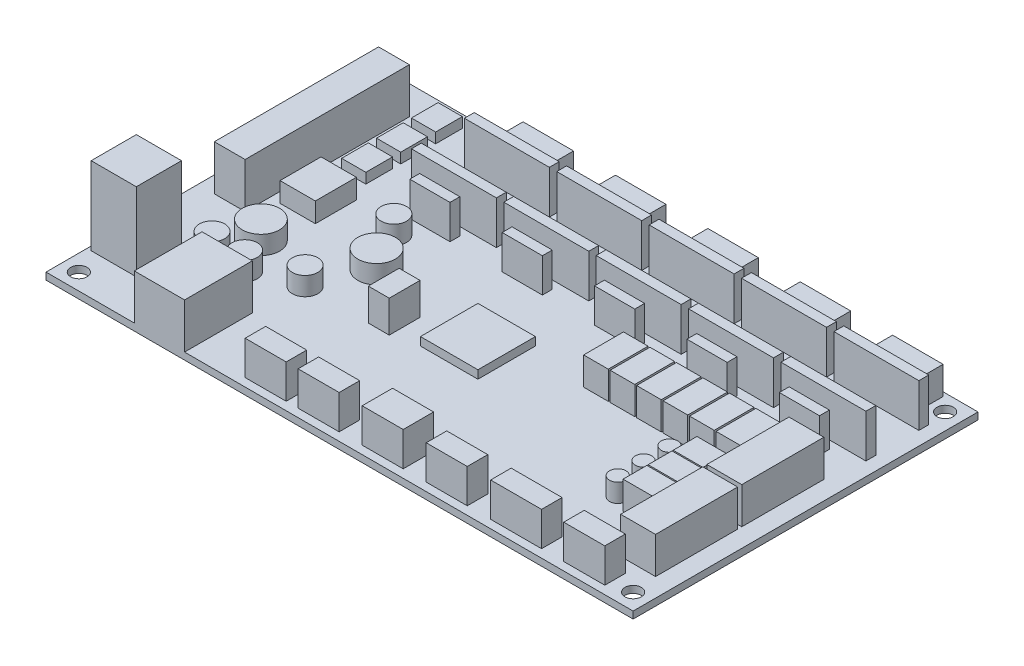
SolidWorks part; units mm, degrees
ref_plane "Front Plane" through (0, 0, 0) normal (0, 0, 1) x (1, 0, 0)
ref_plane "Top Plane" through (0, 0, 0) normal (0, 1, 0) x (1, 0, 0)
ref_plane "Right Plane" through (0, 0, 0) normal (1, 0, 0) x (0, 0, -1)
sketch "PCB" plane through (0, 0, 0) normal (0, 1, 0) x (1, 0, 0)
  line L0 (-71.5, 0) -> (71.5, 0) construction
  line L1 (-71.5, 42) -> (71.5, 42)
  line L2 (-71.5, 42) -> (-71.5, -42)
  line L3 (-71.5, -42) -> (71.5, -42)
  line L4 (71.5, 42) -> (71.5, -42)
  line L5 (0, 42) -> (0, -42) construction
  circle A0 centre (-67.5, -38) radius 2
  circle A1 centre (-67.5, 38) radius 2
  circle A2 centre (67.5, -38) radius 2
  circle A3 centre (67.5, 38) radius 2
  point P0 (0, 0)
  dimension "D3" = 4
  dimension "D1" = 84
  dimension "D2" = 143
  dimension "D4" = 4
  dimension "D5" = 4
extrude "Boss-PCB" add sketch "PCB" along normal blind 1.7
sketch "BlueConnector" plane through (0, 1.7, 0) normal (0, 1, 0) x (1, 0, 0)
  line L0 (71.5, 42) -> (-71.5, 42) construction
  line L1 (-67.5, -5) -> (-60, -5)
  line L2 (-67.5, -5) -> (-67.5, 35)
  line L3 (-67.5, 35) -> (-60, 35)
  line L4 (-60, -5) -> (-60, 35)
  line L5 (-67.5, -5) -> (-60, 35) construction
  line L6 (-67.5, 35) -> (-60, -5) construction
  line L7 (-71.5, 42) -> (-71.5, -42) construction
  point P0 (-63.75, 15)
  dimension "D1" = 40
  dimension "D2" = 7.5
  dimension "D3" = 7
  dimension "D4" = 4
extrude "Boss-BlueConnector" add sketch "BlueConnector" along normal blind 11
sketch "GreenConnector" plane through (0, 1.7, 0) normal (0, 1, 0) x (1, 0, 0)
  line L0 (-71.5, 42) -> (-71.5, -42) construction
  line L1 (-70.5, -21) -> (-59.5, -21)
  line L2 (-70.5, -21) -> (-70.5, -32)
  line L3 (-70.5, -32) -> (-59.5, -32)
  line L4 (-59.5, -21) -> (-59.5, -32)
  line L5 (-70.5, -21) -> (-59.5, -32) construction
  line L6 (-70.5, -32) -> (-59.5, -21) construction
  line L7 (-71.5, -42) -> (71.5, -42) construction
  point P0 (-65, -26.5)
  dimension "D1" = 11
  dimension "D2" = 11
  dimension "D3" = 1
  dimension "D4" = 10
extrude "Boss-GreenConnector" add sketch "GreenConnector" along normal blind 19
sketch "Usb" plane through (0, 1.7, 0) normal (0, 1, 0) x (1, 0, 0)
  line L0 (-71.5, -42) -> (71.5, -42) construction
  line L1 (-50, -25.5) -> (-37.75, -25.5)
  line L2 (-50, -25.5) -> (-50, -42)
  line L3 (-50, -42) -> (-37.75, -42)
  line L4 (-37.75, -25.5) -> (-37.75, -42)
  line L5 (-50, -25.5) -> (-37.75, -42) construction
  line L6 (-50, -42) -> (-37.75, -25.5) construction
  line L7 (-71.5, 42) -> (-71.5, -42) construction
  point P0 (-43.875, -33.75)
  dimension "D1" = 12.25
  dimension "D2" = 16.5
  dimension "D3" = 21.5
extrude "Boss-Usb" add sketch "Usb" along normal blind 11
sketch "DriverSockets" plane through (0, 1.7, 0) normal (0, 1, 0) x (1, 0, 0)
  line L0 (71.5, 42) -> (-71.5, 42) construction
  line L1 (-42.5, 33.3) -> (-21.8, 33.3)
  line L2 (-42.5, 33.3) -> (-42.5, 30.9)
  line L3 (-42.5, 30.9) -> (-21.8, 30.9)
  line L4 (-21.8, 33.3) -> (-21.8, 30.9)
  line L5 (-42.5, 33.3) -> (-21.8, 30.9) construction
  line L6 (-42.5, 30.9) -> (-21.8, 33.3) construction
  line L7 (-42.5, 20.4) -> (-21.8, 20.4)
  line L8 (-42.5, 20.4) -> (-42.5, 18)
  line L9 (-42.5, 18) -> (-21.8, 18)
  line L10 (-21.8, 20.4) -> (-21.8, 18)
  line L11 (-42.5, 20.4) -> (-21.8, 18) construction
  line L12 (-42.5, 18) -> (-21.8, 20.4) construction
  line L13 (-71.5, 42) -> (-71.5, -42) construction
  line L14 (-20, 30.9) -> (0.7, 30.9)
  line L15 (-20, 33.3) -> (-20, 30.9)
  line L16 (-20, 33.3) -> (0.7, 33.3)
  line L17 (0.7, 33.3) -> (0.7, 30.9)
  line L18 (0.7, 20.4) -> (0.7, 18)
  line L19 (-20, 20.4) -> (0.7, 20.4)
  line L20 (-20, 18) -> (0.7, 18)
  line L21 (-20, 20.4) -> (-20, 18)
  line L22 (2.5, 30.9) -> (23.2, 30.9)
  line L23 (2.5, 33.3) -> (2.5, 30.9)
  line L24 (2.5, 33.3) -> (23.2, 33.3)
  line L25 (23.2, 33.3) -> (23.2, 30.9)
  line L26 (23.2, 20.4) -> (23.2, 18)
  line L27 (2.5, 20.4) -> (23.2, 20.4)
  line L28 (2.5, 18) -> (23.2, 18)
  line L29 (2.5, 20.4) -> (2.5, 18)
  line L30 (25, 30.9) -> (45.7, 30.9)
  line L31 (25, 33.3) -> (25, 30.9)
  line L32 (25, 33.3) -> (45.7, 33.3)
  line L33 (45.7, 33.3) -> (45.7, 30.9)
  line L34 (45.7, 20.4) -> (45.7, 18)
  line L35 (25, 20.4) -> (45.7, 20.4)
  line L36 (25, 18) -> (45.7, 18)
  line L37 (25, 20.4) -> (25, 18)
  line L38 (47.5, 30.9) -> (68.2, 30.9)
  line L39 (47.5, 33.3) -> (47.5, 30.9)
  line L40 (47.5, 33.3) -> (68.2, 33.3)
  line L41 (68.2, 33.3) -> (68.2, 30.9)
  line L42 (68.2, 20.4) -> (68.2, 18)
  line L43 (47.5, 20.4) -> (68.2, 20.4)
  line L44 (47.5, 18) -> (68.2, 18)
  line L45 (47.5, 20.4) -> (47.5, 18)
  point P0 (-32.15, 32.1)
  point P5 (-32.15, 19.2)
  dimension "D1" = 10.5
  dimension "D2" = 2.4
  dimension "D3" = 20.7
  dimension "D4" = 8.7
  dimension "D5" = 29
  dimension "D6" = 5
extrude "Boss-DriverSockets" add sketch "DriverSockets" along normal blind 10.5
sketch "NemaSockets" plane through (0, 1.7, 0) normal (0, 1, 0) x (1, 0, 0)
  line L0 (71.5, 42) -> (-71.5, 42) construction
  line L1 (-38.3, 41) -> (-26, 41)
  line L2 (-38.3, 41) -> (-38.3, 35.3)
  line L3 (-38.3, 35.3) -> (-26, 35.3)
  line L4 (-26, 41) -> (-26, 35.3)
  line L5 (-38.3, 41) -> (-26, 35.3) construction
  line L6 (-38.3, 35.3) -> (-26, 41) construction
  line L7 (-71.5, 42) -> (-71.5, -42) construction
  line L8 (-15.8, 41) -> (-3.5, 41)
  line L9 (-15.8, 41) -> (-15.8, 35.3)
  line L10 (-15.8, 35.3) -> (-3.5, 35.3)
  line L11 (-3.5, 41) -> (-3.5, 35.3)
  line L12 (6.7, 41) -> (19, 41)
  line L13 (6.7, 41) -> (6.7, 35.3)
  line L14 (6.7, 35.3) -> (19, 35.3)
  line L15 (19, 41) -> (19, 35.3)
  line L16 (29.2, 41) -> (41.5, 41)
  line L17 (29.2, 41) -> (29.2, 35.3)
  line L18 (29.2, 35.3) -> (41.5, 35.3)
  line L19 (41.5, 41) -> (41.5, 35.3)
  line L20 (51.7, 41) -> (64, 41)
  line L21 (51.7, 41) -> (51.7, 35.3)
  line L22 (51.7, 35.3) -> (64, 35.3)
  line L23 (64, 41) -> (64, 35.3)
  point P0 (-32.15, 38.15)
  dimension "D1" = 5.7
  dimension "D2" = 12.3
  dimension "D3" = 1
  dimension "D4" = 33.2
  dimension "D5" = 5
extrude "Boss-NemaSockets" add sketch "NemaSockets" along normal blind 6.8
sketch "Sketch2" plane through (0, 1.7, 0) normal (0, 1, 0) x (1, 0, 0)
  line L0 (-37.75, -42) -> (71.5, -42) construction
  line L1 (66.9613, 9) -> (58.4613, 9)
  line L2 (66.9613, 9) -> (66.9613, -11)
  line L3 (66.9613, -11) -> (58.4613, -11)
  line L4 (58.4613, 9) -> (58.4613, -11)
  line L5 (66.9613, 9) -> (58.4613, -11) construction
  line L6 (66.9613, -11) -> (58.4613, 9) construction
  line L7 (66.9613, -32) -> (58.4613, -32)
  line L8 (66.9613, -32) -> (66.9613, -12)
  line L9 (66.9613, -12) -> (58.4613, -12)
  line L10 (58.4613, -32) -> (58.4613, -12)
  line L11 (66.9613, -32) -> (58.4613, -12) construction
  line L12 (66.9613, -12) -> (58.4613, -32) construction
  point P0 (62.7113, -1)
  point P5 (62.7113, -22)
  dimension "D1" = 10
  dimension "D2" = 20
  dimension "D3" = 8.5
  dimension "D4" = 1
extrude "Boss-Extrude2" add sketch "Sketch2" along normal blind 8.9
sketch "Sketch3" plane through (0, 1.7, 0) normal (0, 1, 0) x (1, 0, 0)
  line L0 (-37.75, -42) -> (71.5, -42) construction
  line L1 (50.5, 8.9) -> (56.5, 8.9)
  line L2 (50.5, 8.9) -> (50.5, -0.8)
  line L3 (50.5, -0.8) -> (56.5, -0.8)
  line L4 (56.5, 8.9) -> (56.5, -0.8)
  line L5 (50.5, 8.9) -> (56.5, -0.8) construction
  line L6 (50.5, -0.8) -> (56.5, 8.9) construction
  line L7 (44.05, -0.8) -> (50.05, -0.8)
  line L8 (44.05, 8.9) -> (44.05, -0.8)
  line L9 (44.05, 8.9) -> (50.05, 8.9)
  line L10 (50.05, 8.9) -> (50.05, -0.8)
  line L11 (37.6, -0.8) -> (43.6, -0.8)
  line L12 (37.6, 8.9) -> (37.6, -0.8)
  line L13 (37.6, 8.9) -> (43.6, 8.9)
  line L14 (43.6, 8.9) -> (43.6, -0.8)
  line L15 (31.15, -0.8) -> (37.15, -0.8)
  line L16 (31.15, 8.9) -> (31.15, -0.8)
  line L17 (31.15, 8.9) -> (37.15, 8.9)
  line L18 (37.15, 8.9) -> (37.15, -0.8)
  line L19 (24.7, -0.8) -> (30.7, -0.8)
  line L20 (24.7, 8.9) -> (24.7, -0.8)
  line L21 (24.7, 8.9) -> (30.7, 8.9)
  line L22 (30.7, 8.9) -> (30.7, -0.8)
  line L23 (18.25, -0.8) -> (24.25, -0.8)
  line L24 (18.25, 8.9) -> (18.25, -0.8)
  line L25 (18.25, 8.9) -> (24.25, 8.9)
  line L26 (24.25, 8.9) -> (24.25, -0.8)
  line L27 (71.5, -42) -> (71.5, 42) construction
  point P0 (53.5, 4.05)
  dimension "D1" = 6
  dimension "D2" = 9.7
  dimension "D3" = 41.2
  dimension "D5" = 15
  dimension "D4" = 6
extrude "Boss-Extrude3" add sketch "Sketch3" along normal blind 6.8
sketch "Sketch4" plane through (0, 1.7, 0) normal (0, 1, 0) x (1, 0, 0)
  line L0 (49.25, -10.3) -> (56.5, -10.3)
  line L1 (49.25, -4.2) -> (56.5, -4.2)
  line L2 (49.25, -4.2) -> (49.25, -10)
  line L3 (49.25, -10) -> (56.5, -10)
  line L4 (56.5, -4.2) -> (56.5, -10)
  line L5 (49.25, -4.2) -> (56.5, -10) construction
  line L6 (49.25, -10) -> (56.5, -4.2) construction
  line L7 (56.5, -10.3) -> (56.5, -16.1)
  line L8 (49.25, -16.1) -> (56.5, -16.1)
  line L9 (49.25, -10.3) -> (49.25, -16.1)
  line L10 (49.25, -16.4) -> (56.5, -16.4)
  line L11 (56.5, -16.4) -> (56.5, -22.2)
  line L12 (49.25, -22.2) -> (56.5, -22.2)
  line L13 (49.25, -16.4) -> (49.25, -22.2)
  line L14 (71.5, -42) -> (71.5, 42) construction
  line L15 (-37.75, -42) -> (71.5, -42) construction
  point P0 (52.875, -7.1)
  dimension "D1" = 5.8
  dimension "D2" = 7.25
  dimension "D4" = 18
  dimension "D5" = 15
  dimension "D6" = 19.8
  dimension "D3" = 3
extrude "Boss-Extrude4" add sketch "Sketch4" along normal blind 6.8
sketch "Sketch5" plane through (0, 1.7, 0) normal (0, 1, 0) x (1, 0, 0)
  circle A0 centre (45.5325, -7.1736) radius 2
  circle A1 centre (45.5325, -13.4736) radius 2
  circle A2 centre (45.5325, -19.7736) radius 2
  circle A3 centre (-36.9279, 8.1532) radius 3.1
  circle A4 centre (-55.3867, -17.6755) radius 3.1
  circle A5 centre (-47.4486, -17.6755) radius 3.1
  circle A6 centre (-36.9279, -13.4736) radius 3.1
  circle A7 centre (-31.771, -1.204) radius 4.5816
  circle A8 centre (-52.013, -9.1421) radius 4.5488
  dimension "D2" = 4
  dimension "D3" = 6.2
  dimension "D1" = 3
extrude "Boss-Extrude5" add sketch "Sketch5" along normal blind 4.5
sketch "Sketch6" plane through (0, 1.7, 0) normal (0, 1, 0) x (1, 0, 0)
  line L0 (71.5, 42) -> (-71.5, 42) construction
  line L1 (-57, 39) -> (-51.1, 39)
  line L2 (-57, 39) -> (-57, 32.5)
  line L3 (-57, 32.5) -> (-51.1, 32.5)
  line L4 (-51.1, 39) -> (-51.1, 32.5)
  line L5 (-57, 39) -> (-51.1, 32.5) construction
  line L6 (-57, 32.5) -> (-51.1, 39) construction
  line L7 (-71.5, 42) -> (-71.5, -42) construction
  line L8 (-51.1, 30.5) -> (-51.1, 24)
  line L9 (-57, 24) -> (-51.1, 24)
  line L10 (-57, 30.5) -> (-57, 24)
  line L11 (-57, 30.5) -> (-51.1, 30.5)
  line L12 (-51.1, 22) -> (-51.1, 15.5)
  line L13 (-57, 15.5) -> (-51.1, 15.5)
  line L14 (-57, 22) -> (-57, 15.5)
  line L15 (-57, 22) -> (-51.1, 22)
  point P0 (-54.05, 35.75)
  dimension "D1" = 6.5
  dimension "D2" = 5.9
  dimension "D3" = 3
  dimension "D4" = 14.5
  dimension "D5" = 3
extrude "Boss-Extrude6" add sketch "Sketch6" along normal blind 2.5
sketch "Sketch7" plane through (0, 1.7, 0) normal (0, 1, 0) x (1, 0, 0)
  line L0 (-71.5, 42) -> (-71.5, -42) construction
  line L1 (-57.5, 11) -> (-48.9, 11)
  line L2 (-57.5, 11) -> (-57.5, 1)
  line L3 (-57.5, 1) -> (-48.9, 1)
  line L4 (-48.9, 11) -> (-48.9, 1)
  line L5 (-57.5, 11) -> (-48.9, 1) construction
  line L6 (-57.5, 1) -> (-48.9, 11) construction
  line L7 (71.5, 42) -> (-71.5, 42) construction
  point P0 (-53.2, 6)
  dimension "D1" = 10
  dimension "D2" = 8.6
  dimension "D3" = 14
  dimension "D4" = 31
extrude "Boss-Extrude7" add sketch "Sketch7" along normal blind 4.8
sketch "Sketch8" plane through (0, 1.7, 0) normal (0, 1, 0) x (1, 0, 0)
  line L0 (71.5, 42) -> (-71.5, 42) construction
  line L1 (-21.5, -6) -> (-16.4, -6)
  line L2 (-21.5, -6) -> (-21.5, -13.5)
  line L3 (-21.5, -13.5) -> (-16.4, -13.5)
  line L4 (-16.4, -6) -> (-16.4, -13.5)
  line L5 (-21.5, -6) -> (-16.4, -13.5) construction
  line L6 (-21.5, -13.5) -> (-16.4, -6) construction
  line L7 (-71.5, 42) -> (-71.5, -42) construction
  point P0 (-18.95, -9.75)
  dimension "D1" = 5.1
  dimension "D2" = 7.5
  dimension "D3" = 48
  dimension "D4" = 50
extrude "Boss-Extrude8" add sketch "Sketch8" along normal blind 7.8
sketch "Sketch9" plane through (0, 1.7, 0) normal (0, 1, 0) x (1, 0, 0)
  line L0 (71.5, 42) -> (-71.5, 42) construction
  line L1 (-10.3, 2) -> (3.7, 2)
  line L2 (-10.3, 2) -> (-10.3, -12)
  line L3 (-10.3, -12) -> (3.7, -12)
  line L4 (3.7, 2) -> (3.7, -12)
  line L5 (-10.3, 2) -> (3.7, -12) construction
  line L6 (-10.3, -12) -> (3.7, 2) construction
  line L7 (-71.5, 42) -> (-71.5, -42) construction
  point P0 (-3.3, -5)
  dimension "D1" = 14
  dimension "D2" = 14
  dimension "D3" = 40
  dimension "D4" = 61.2
extrude "Boss-Extrude9" add sketch "Sketch9" along normal blind 2
sketch "Sketch10" plane through (0, 1.7, 0) normal (0, 1, 0) x (1, 0, 0)
  line L0 (71.5, -42) -> (71.5, 42) construction
  line L1 (-25, -35) -> (-15, -35)
  line L2 (-25, -35) -> (-25, -40)
  line L3 (-25, -40) -> (-15, -40)
  line L4 (-15, -35) -> (-15, -40)
  line L5 (-25, -35) -> (-15, -40) construction
  line L6 (-25, -40) -> (-15, -35) construction
  line L7 (-12.1, -35) -> (-2.1, -35)
  line L8 (-12.1, -35) -> (-12.1, -40)
  line L9 (-12.1, -40) -> (-2.1, -40)
  line L10 (-2.1, -35) -> (-2.1, -40)
  line L11 (-12.1, -35) -> (-2.1, -40) construction
  line L12 (-12.1, -40) -> (-2.1, -35) construction
  line L13 (19.1, -35) -> (29.1, -35)
  line L14 (19.1, -35) -> (19.1, -40)
  line L15 (19.1, -40) -> (29.1, -40)
  line L16 (29.1, -35) -> (29.1, -40)
  line L17 (19.1, -35) -> (29.1, -40) construction
  line L18 (19.1, -40) -> (29.1, -35) construction
  line L19 (3.5, -32.6) -> (13.5, -32.6)
  line L20 (3.5, -32.6) -> (3.5, -40)
  line L21 (3.5, -40) -> (13.5, -40)
  line L22 (13.5, -32.6) -> (13.5, -40)
  line L23 (3.5, -32.6) -> (13.5, -40) construction
  line L24 (3.5, -40) -> (13.5, -32.6) construction
  line L25 (34.8, -35) -> (47.2, -35)
  line L26 (34.8, -35) -> (34.8, -40)
  line L27 (34.8, -40) -> (47.2, -40)
  line L28 (47.2, -35) -> (47.2, -40)
  line L29 (34.8, -35) -> (47.2, -40) construction
  line L30 (34.8, -40) -> (47.2, -35) construction
  line L31 (52.6, -35) -> (62.6, -35)
  line L32 (52.6, -35) -> (52.6, -40)
  line L33 (52.6, -40) -> (62.6, -40)
  line L34 (62.6, -35) -> (62.6, -40)
  line L35 (52.6, -35) -> (62.6, -40) construction
  line L36 (52.6, -40) -> (62.6, -35) construction
  line L37 (-37.75, -42) -> (71.5, -42) construction
  point P0 (-20, -37.5)
  point P5 (-7.1, -37.5)
  point P10 (24.1, -37.5)
  point P15 (8.5, -36.3)
  point P20 (41, -37.5)
  point P25 (57.6, -37.5)
  dimension "D1" = 10
  dimension "D2" = 5
  dimension "D3" = 7.4
  dimension "D4" = 42.4
  dimension "D5" = 8.9
  dimension "D6" = 24.3
  dimension "D7" = 58
  dimension "D8" = 12.4
  dimension "D9" = 73.6
  dimension "D10" = 86.5
  dimension "D11" = 2
extrude "Boss-Extrude10" add sketch "Sketch10" along normal blind 8.3
sketch "Sketch11" plane through (0, 1.7, 0) normal (0, 1, 0) x (1, 0, 0)
  line L0 (-16, 13.6) -> (-6.2, 13.6)
  line L1 (-38.5, 16) -> (-28.7, 16)
  line L2 (-38.5, 16) -> (-38.5, 13.6)
  line L3 (-38.5, 13.6) -> (-28.7, 13.6)
  line L4 (-28.7, 16) -> (-28.7, 13.6)
  line L5 (-38.5, 16) -> (-28.7, 13.6) construction
  line L6 (-38.5, 13.6) -> (-28.7, 16) construction
  line L7 (-6.2, 16) -> (-6.2, 13.6)
  line L8 (-16, 16) -> (-6.2, 16)
  line L9 (-16, 16) -> (-16, 13.6)
  line L10 (6.5, 13.6) -> (16.3, 13.6)
  line L11 (16.3, 16) -> (16.3, 13.6)
  line L12 (6.5, 16) -> (16.3, 16)
  line L13 (6.5, 16) -> (6.5, 13.6)
  line L14 (29, 13.6) -> (38.8, 13.6)
  line L15 (38.8, 16) -> (38.8, 13.6)
  line L16 (29, 16) -> (38.8, 16)
  line L17 (29, 16) -> (29, 13.6)
  line L18 (51.5, 13.6) -> (61.3, 13.6)
  line L19 (61.3, 16) -> (61.3, 13.6)
  line L20 (51.5, 16) -> (61.3, 16)
  line L21 (51.5, 16) -> (51.5, 13.6)
  line L22 (-71.5, 42) -> (-71.5, -42) construction
  line L23 (71.5, 42) -> (-71.5, 42) construction
  point P0 (-33.6, 14.8)
  dimension "D1" = 2.4
  dimension "D2" = 9.8
  dimension "D4" = 33
  dimension "D5" = 26
  dimension "D3" = 5
extrude "Boss-Extrude11" add sketch "Sketch11" along normal blind 8.3
